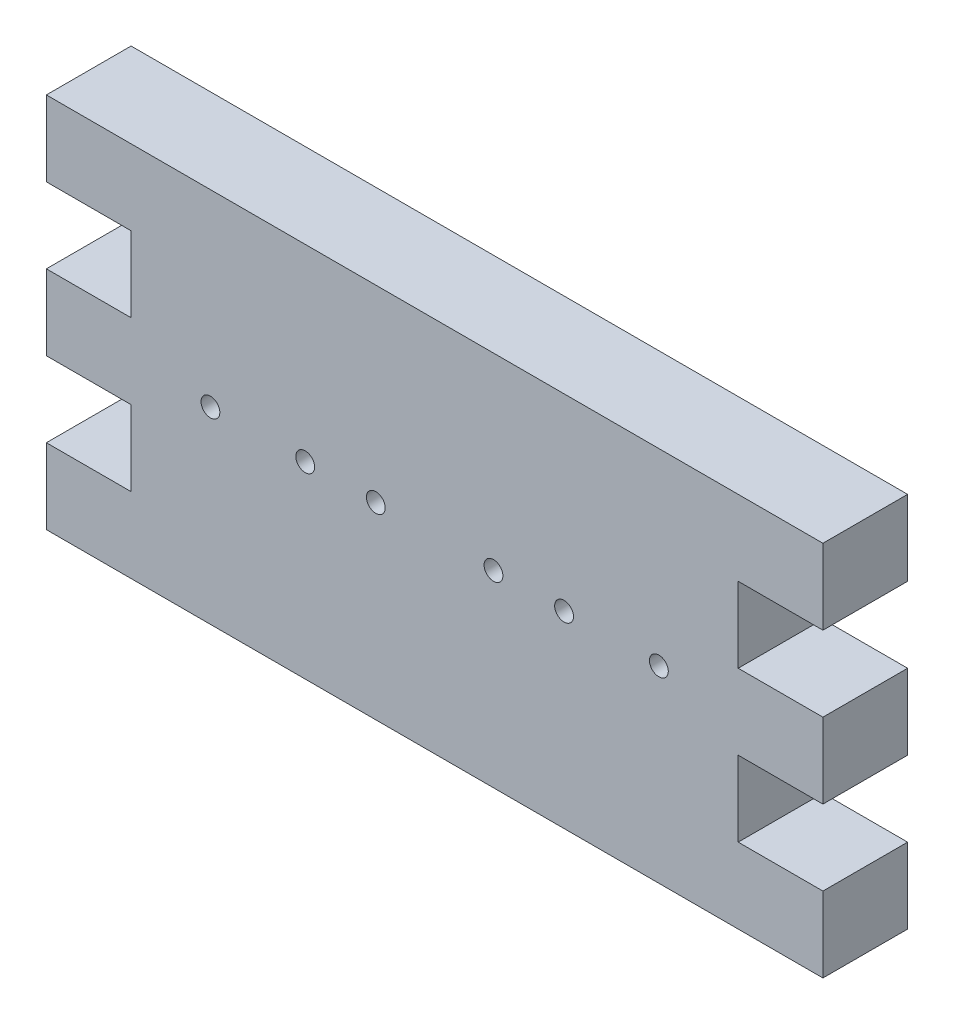
SolidWorks part; units mm, degrees
ref_plane "Front Plane" through (0, 0, 0) normal (0, 0, 1) x (1, 0, 0)
ref_plane "Top Plane" through (0, 0, 0) normal (0, 1, 0) x (1, 0, 0)
ref_plane "Right Plane" through (0, 0, 0) normal (1, 0, 0) x (0, 0, -1)
sketch "Sketch1" plane through (0, 0, 0) normal (0, 0, 1) x (1, 0, 0)
  line L0 (-1017.5, -10) -> (48982.5, -10) construction
  line L1 (-42.5, -50) -> (122.5, -50)
  line L2 (-42.5, -50) -> (-42.5, -34)
  line L3 (-42.5, 30) -> (122.5, 30)
  line L4 (122.5, -50) -> (122.5, -34)
  line L5 (-24.5, -34) -> (-24.5, -18)
  line L6 (-42.5, -34) -> (-24.5, -34)
  line L7 (-17.5, -20) -> (-17.5, 0) construction
  line L8 (40, -811.5916) -> (40, 49188.4084) construction
  line L9 (44, 250.3966) -> (36, 250.3966) construction
  line L10 (-42.5, -18) -> (-24.5, -18)
  line L11 (-42.5, -2) -> (-24.5, -2)
  line L12 (-42.5, 14) -> (-24.5, 14)
  line L13 (-42.5, -18) -> (-42.5, -2)
  line L14 (-24.5, -2) -> (-24.5, 14)
  line L15 (-42.5, 14) -> (-42.5, 30)
  line L16 (104.5, -2) -> (104.5, 14)
  line L17 (122.5, 14) -> (104.5, 14)
  line L18 (122.5, -2) -> (104.5, -2)
  line L19 (122.5, -18) -> (104.5, -18)
  line L20 (122.5, -34) -> (104.5, -34)
  line L21 (104.5, -34) -> (104.5, -18)
  line L22 (122.5, -18) -> (122.5, -2)
  line L23 (122.5, 14) -> (122.5, 30)
  circle A0 centre (-7.6457, -10) radius 2
  circle A1 centre (12.5, -10) radius 2
  circle A2 centre (27.5, -10) radius 2
  circle A3 centre (52.5, -10) radius 2
  circle A4 centre (67.5, -10) radius 2
  circle A5 centre (87.6457, -10) radius 2
  point P0 (40, -10)
  point P10 (-17.5, -10)
  point P15 (40, 250.3966)
  point P24 (-42.5, -10)
  point P25 (40, -50)
  dimension "D3" = 4
  dimension "D1" = 16
  dimension "D2" = 165
  dimension "D4" = 18
extrude "Boss-Extrude1" add sketch "Sketch1" along normal blind 18
